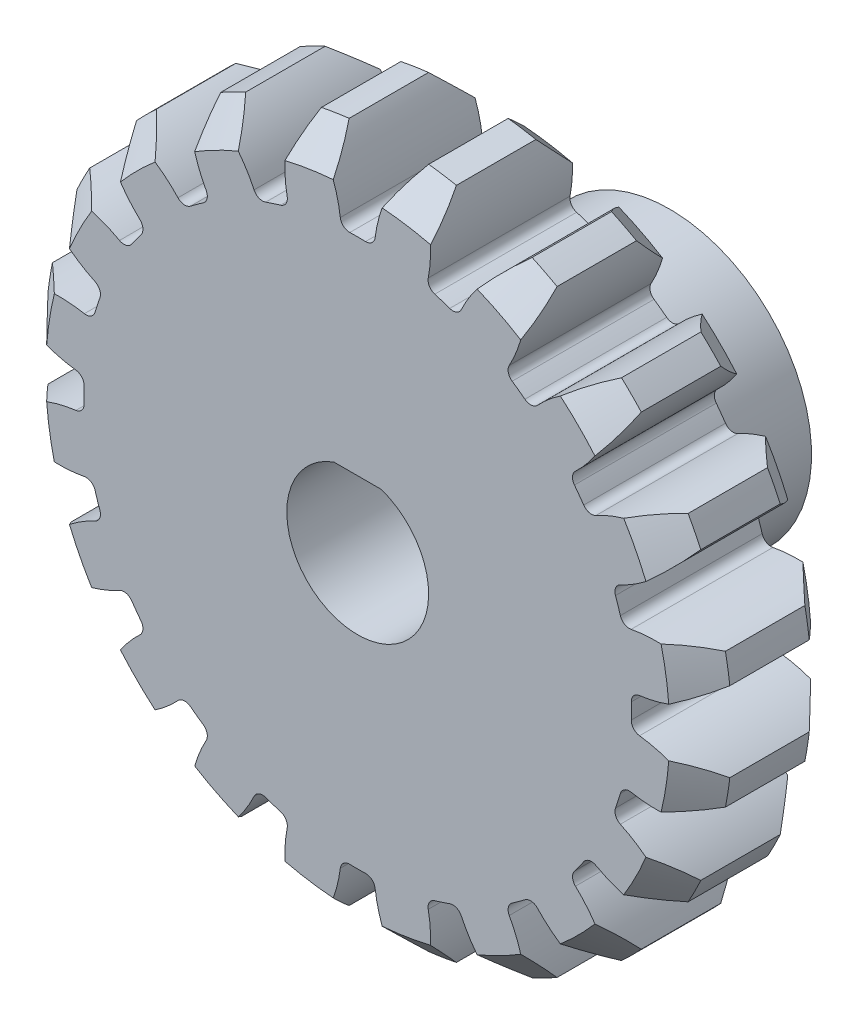
SolidWorks part; units mm, degrees
ref_plane "Front Plane" through (0, 0, 0) normal (0, 0, 1) x (1, 0, 0)
ref_plane "Top Plane" through (0, 0, 0) normal (0, 1, 0) x (1, 0, 0)
ref_plane "Right Plane" through (0, 0, 0) normal (1, 0, 0) x (0, 0, -1)
sketch "Sketch1" plane through (0, 0, 0) normal (0, 0, 1) x (1, 0, 0)
  circle A0 centre (0, 0) radius 22 construction
  circle A1 centre (0, 0) radius 24.2
  dimension "D1" = 44
  dimension "D2" = 48.4
extrude "Boss-Extrude1" add sketch "Sketch1" along normal mid plane 10
sketch "Sketch2" plane through (0, 0, 0) normal (0, 0, 1) x (1, 0, 0)
  line L0 (0, 0) -> (0, 24.2) construction
  line L1 (0, 0) -> (7.4782, 23.0156) construction
  line L2 (0, 0) -> (3.7857, 23.9021) construction
  line L3 (-1.1717, 19.2644) -> (0, 0) construction
  line L4 (-1.7261, 21.9322) -> (1.7261, 21.9322) construction
  line L5 (1.7261, 21.9322) -> (5.1358, 21.3921) construction
  line L6 (-2.5042, 24.0701) -> (0, 17.1898) construction
  circle A0 centre (0, 0) radius 19.8 construction
  circle A2 centre (0, 0) radius 24.2 construction
  arc A3 (-2.8061, 24.0368) -> (-1.1717, 19.2644) centre (-10.6375, 18.6887) cw
  circle A4 centre (0, 0) radius 24.2 construction
  arc A5 (2.8061, 24.0368) -> (1.1717, 19.2644) centre (10.6375, 18.6887) ccw
  circle A6 centre (0, 0) radius 22 construction
  arc A7 (1.1717, 19.2644) -> (-1.1717, 19.2644) centre (0, 0) ccw
  arc A8 (2.8061, 24.0368) -> (-2.8061, 24.0368) centre (0, 0) ccw
  dimension "D1" = 18
  dimension "D2" = 4.4
  dimension "D4" = 20
  dimension "D3" = 0.5
extrude "Cut-Extrude1" cut sketch "Sketch2" against normal through all both and the other way through all contours A5 A8 A3 A7
fillet "Fillet1" radius 0.66 2 edges at (1.1717, 19.2644, 0) (-1.1717, 19.2644, 0)
chamfer "Chamfer1" distance 2.2 angle 45 2 edges at (0, -24.2, -5) (0, -24.2, 5)
pattern_circular "CirPattern1" count 20 over 360 about axis through (0, 0, 0) along (0, 0, 1) of "Fillet1", "Cut-Extrude1"
sketch "Sketch3" plane through (0, 0, 5) normal (0, 0, 1) x (1, 0, 0)
  line L2 (-2, 4.5826) -> (-2, 7)
  line L3 (-2, 7) -> (2, 7)
  line L4 (2, 4.5826) -> (2, 7)
  arc A0 (-2, 4.5826) -> (2, 4.5826) centre (0, 0) ccw
  point P3 (0, 5)
  point P5 (0, 7)
  dimension "D1" = 10
  dimension "D2" = 2
  dimension "D3" = 4
extrude "Cut-Extrude2" cut sketch "Sketch3" against normal through all
fillet "Fillet2" radius 0.2 12 edges at (0, -5, 5) (0, -5, -5) (-2, 4.5826, 0) (2, 4.5826, 0) (0, 7, -5) (0, 7, 5) (-2, 7, 0) (-2, 5.7913, -5) (-2, 5.7913, 5) (2, 5.7913, -5) (2, 7, 0) (2, 5.7913, 5)
sketch "Sketch5" plane through (0, 0, 0) normal (0, 0, 1) x (1, 0, 0)
  circle A0 centre (0, 0) radius 22
sketch "Sketch6" plane through (0, 0, -5) normal (0, 0, -1) x (-1, 0, 0)
  line L0 (-1.6733, 4.7117) -> (1.6733, 4.7117)
  circle A0 centre (0, 0) radius 10
  arc A2 (-1.6733, 4.7117) -> (1.6733, 4.7117) centre (0, 0) ccw
  point P6 (0, 4.7117)
  dimension "D1" = 10
  dimension "D2" = 5
  dimension "D3" = 4.7117
extrude "Boss-Extrude2" add sketch "Sketch6" along normal blind 12 and the other way up to surface (10 mm away) other way up to face at (0, 0, 5)
sketch "Sketch8" plane through (0, 0, 0) normal (0, 1, 0) x (1, 0, 0)
  line L0 (10, 5) -> (10, 17) construction
  line L1 (10, 17) -> (-10, 17) construction
  circle A0 centre (0, 11) radius 1.15
  dimension "D1" = 2.3
  dimension "D2" = 10
  dimension "D3" = 6
extrude "Cut-Extrude3" cut sketch "Sketch8" along normal blind 12
equation "\"Module\"= 2.2"
equation "\"Number of Teeth\"= 20'Number of Teeth"
equation "\"Pressure Angle\"= 20"
equation "\"D1@Sketch1\"=\"Module\" * \"Number of Teeth\""
equation "\"D2@Sketch1\"=( \"Number of Teeth\" + 2) * \"Module\""
equation "\"D1@Sketch2\"=360 / \"Number of Teeth\""
equation "\"D2@Sketch2\"= \"Module\" * 2"
equation "\"D4@Sketch2\"=\"Pressure Angle\""
equation "\"D1@Fillet1\"=0.3 * \"Module\""
equation "\"D1@CirPattern1\"= \"Number of Teeth\""
equation "\"D1@Chamfer1\"= \"Module\""
equation "\"Gear Thickness\"= 10"
equation "\"D1@Boss-Extrude1\"= \"Gear Thickness\""
